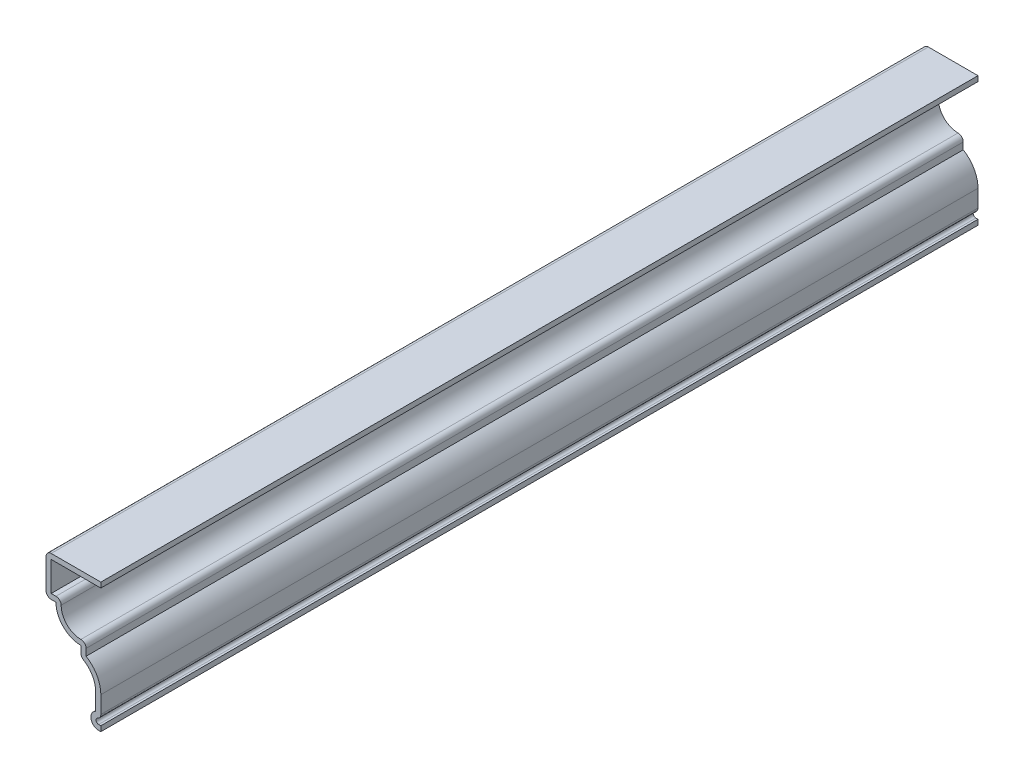
SolidWorks part; units mm, degrees
ref_plane "Front Plane" through (0, 0, 0) normal (0, 0, 1) x (1, 0, 0)
ref_plane "Top Plane" through (0, 0, 0) normal (0, 1, 0) x (1, 0, 0)
ref_plane "Right Plane" through (0, 0, 0) normal (1, 0, 0) x (0, 0, -1)
sketch "Sketch1" plane through (0, 0, 0) normal (0, 0, 1) x (1, 0, 0)
  line L0 (0, 0) -> (0, 41.275) construction
  line L1 (0, 0) -> (9.7419, 0) construction
  line L2 (-1.651, 4.7625) -> (-1.651, 10.2157)
  line L3 (-6.35, 17.4625) -> (-6.35, 20.6375)
  line L4 (-14.2875, 28.575) -> (-17.4625, 28.575)
  line L5 (-17.4625, 28.575) -> (-17.4625, 41.275)
  line L6 (-17.4625, 41.275) -> (0, 41.275)
  line L7 (-3.175, 7.8109) -> (-3.175, -2.0304) construction
  line L8 (-0.6985, 0) -> (0, 0)
  arc A0 (-1.651, 4.7625) -> (-0.6985, 0) centre (-0.6985, 2.4765) ccw
  arc A1 (-1.651, 10.2157) -> (-6.35, 17.4625) centre (-9.5885, 10.2157) ccw
  arc A2 (-6.35, 20.6375) -> (-14.2875, 28.575) centre (-6.35, 28.575) cw
  dimension "D3" = 3.175
  dimension "D5" = 1.651
  dimension "D1" = 41.275
  dimension "D2" = 17.4625
  dimension "D4" = 3.175
  dimension "D6" = 3.175
  dimension "D7" = 7.9375
  dimension "D8" = 12.7
  dimension "D9" = 4.7625
  dimension "D10" = 12.7
extrude "Extrude-Thin2" add sketch "Sketch1" against normal blind 279.4 thin
fillet "Fillet1" radius 1.651 6 edges at (-6.35, 17.4625, -139.7) (-4.699, 22.5092, -139.7) (-12.4158, 30.226, -139.7) (-17.4625, 28.575, -139.7) (-17.4625, 41.275, -139.7) (0, 2.9164, -139.7)
